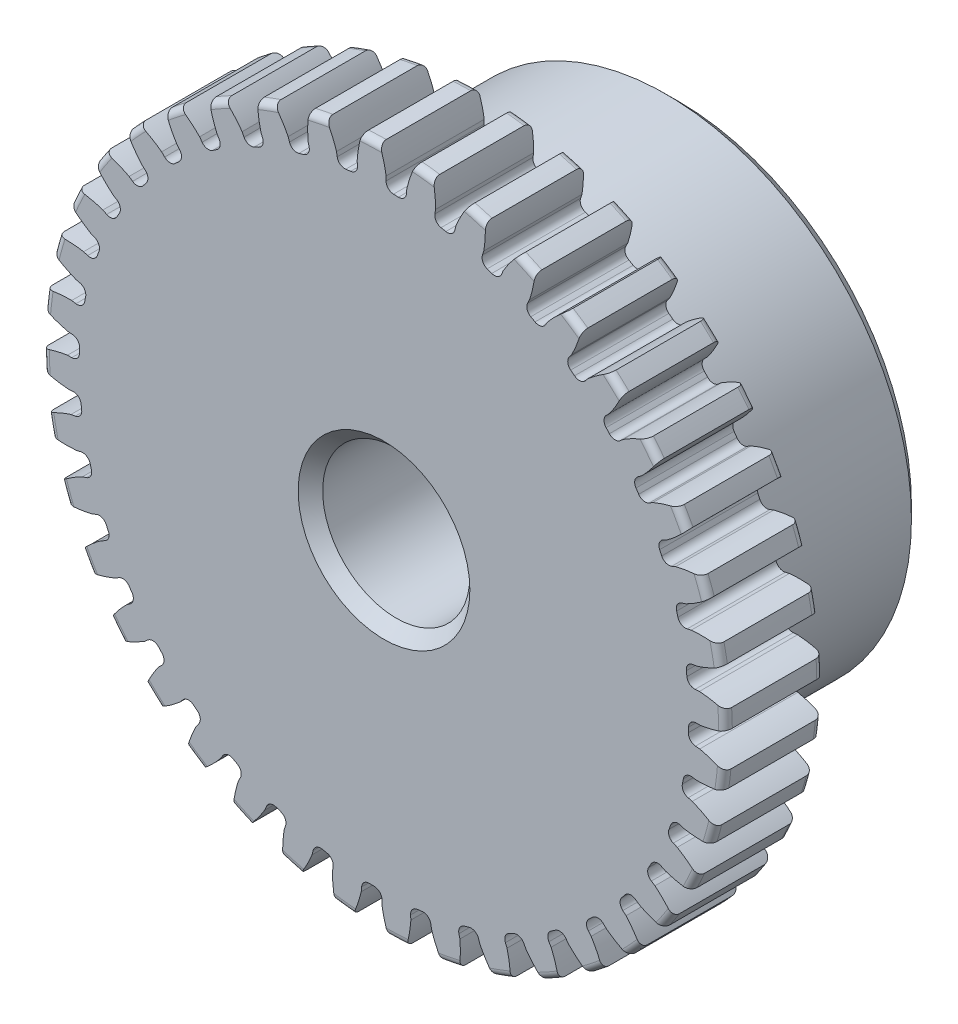
SolidWorks part; units mm, degrees
ref_plane "Front" through (0, 0, 0) normal (0, 0, 1) x (1, 0, 0)
ref_plane "Top" through (0, 0, 0) normal (0, 1, 0) x (1, 0, 0)
ref_plane "Right" through (0, 0, 0) normal (1, 0, 0) x (0, 0, -1)
sketch "Sketch1" plane through (0, 0, 0) normal (0, 0, 1) x (1, 0, 0)
  line L0 (-508, 0) -> (508, 0) construction
  circle A0 centre (0, 0) radius 11.049
  circle A1 centre (0, 0) radius 10.5791 construction
  circle A3 centre (0, 0) radius 9.8589 construction
  dimension "D1" = 1.1901
  dimension "OD" = 22.098
  dimension "Ptich Dia" = 21.1582
  dimension "Root Dia" = 19.7177
  dimension "D3" = 0.4699
  dimension "Number of Teeth" = 1016
extrude "Boss-Extrude1" add sketch "Sketch1" against normal blind 3.175
sketch "Sketch2" plane through (0, 0, 0) normal (1, 0, 0) x (0, 0, -1)
  line L0 (3.175, 0) -> (9.525, 0)
  line L1 (3.175, 0) -> (3.175, 7.9375)
  line L2 (3.175, 7.9375) -> (9.525, 7.9375)
  line L3 (9.525, 7.9375) -> (9.525, 0)
  point P5 (9.525, -7.9375)
  point P6 (0, -11.049)
  point P7 (3.175, -11.049)
  point P9 (0, 11.049)
  dimension "Face Wd" = 3.175
  dimension "B Hub Dia" = 15.875
  dimension "D O'all Lg." = 9.525
revolve "Revolve1" add sketch "Sketch2" angle 360 about L0
fillet "Fillet2" radius 0.221 3 edges at (11.049, 0, -3.175) (11.049, 0, 0) (7.9375, 0, -3.175)
sketch "Sketch3" plane through (0, 0, 0) normal (0, 0, 1) x (1, 0, 0)
  line L0 (0, 0) -> (0, 11.049) construction
  line L1 (-2.5644, 9.9159) -> (0, 10.5791)
  line L2 (-9.5921, 10.5791) -> (9.5921, 10.5791) construction
  line L3 (-9.2865, 8.1774) -> (9.2865, 12.9808) construction
  line L4 (-2.5644, 9.9159) -> (0, 0) construction
  line L5 (-6.541, 7.8814) -> (0, 0) construction
  line L6 (-6.541, 7.8814) -> (-1.0572, 12.4326) construction
  line L7 (-1.7882, 10.0848) -> (0, 0) construction
  line L8 (-1.7882, 10.0848) -> (0.0375, 10.4085) construction
  arc A0 (-2.5644, 9.9159) -> (-6.541, 7.8814) centre (0, 0) ccw
  circle A1 centre (0, 0) radius 10.5791 construction
  circle A2 centre (0, 0) radius 10.2421 construction
  arc A3 (-2.5644, 9.9159) -> (-1.7882, 10.0848) centre (0, 0) cw
  circle A4 centre (0, 0) radius 11.049 construction
  point P6 (0, 10.5791)
  dimension "D1" = 2.6488
  dimension "Pressure Angle" = 14.5
  dimension "D2" = 4.503
  dimension "D3" = 7.1263
  dimension "D4" = 0.7946
  dimension "D5" = 1.8542
sketch "Sketch4" plane through (0, 0, 0) normal (0, 0, 1) x (1, 0, 0)
  line L0 (0, 0) -> (0.415, 10.5628) construction
  line L1 (0.0664, 10.2419) -> (0.0664, 9.8586)
  line L2 (0, 10.5791) -> (0.83, 10.5465) construction
  line L3 (0.7373, 10.2156) -> (0.7073, 9.8334)
  line L4 (0.0664, 9.8586) -> (0, 0) construction
  line L5 (0, 0) -> (0, 11.049) construction
  line L6 (-6.541, 7.8814) -> (-1.0572, 12.4326) construction
  line L7 (-6.541, 7.8814) -> (-1.0572, 12.4326) construction
  arc A0 (0.7073, 9.8334) -> (0.0664, 9.8586) centre (0, 0) ccw
  arc A1 (0, 10.5791) -> (0.83, 10.5465) centre (0, 0) cw construction
  circle A2 centre (0, 0) radius 10.5791 construction
  circle A3 centre (0, 0) radius 10.2421 construction
  circle A4 centre (0, 0) radius 9.8589 construction
  arc A5 (2.0294, 12.3113) -> (-1.0572, 12.4326) centre (0, 0) ccw
  spline S0 degree 2 poles (-1.0572, 12.4326) (-0.119, 11.4678) (0.0664, 10.2419) knots 0 0 0 1 1 1
  spline S1 degree 2 poles (2.0294, 12.3113) (1.0184, 11.4231) (0.7373, 10.2156) knots 0 0 0 1 1 1
  dimension "D1" = 0.8309
extrude "Cut-Extrude1" cut sketch "Sketch4" against normal through all
fillet "Fillet1" radius 0.2493 2 edges at (0.7073, 9.8334, -1.5875) (0.0664, 9.8586, -1.5875)
pattern_circular "CirPattern1" count 40 over 360 about axis through (0, 0, -3.175) along (0, 0, 1) of "Cut-Extrude1", "Fillet1"
sketch "Sketch5" plane through (0, 0, 0) normal (0, 0, 1) x (1, 0, 0)
  circle A0 centre (0, 0) radius 2.3813
  circle A1 centre (0, 0) radius 1.5875 construction
  dimension "Bore Min" = 4.7625
  dimension "Bore Max" = 3.175
extrude "Cut-Extrude2" cut sketch "Sketch5" against normal through all
chamfer "Chamfer1" distance 0.3969 angle 45 3 edges at (7.9375, 0, -9.525) (2.3813, 0, 0) (2.3813, 0, -9.525)
sketch "Pitch Dia" plane through (0, 0, 0) normal (0, 0, 1) x (1, 0, 0)
  circle A0 centre (0, 0) radius 10.5791 construction
  circle A1 centre (0, 0) radius 10.5791 construction
equation "\"D1@Boss-Extrude1\" = \"Face Wd@Sketch2\""
equation "\"D2@Sketch3\" = \"D1@Sketch3\"*1.7"
equation "\"D3@Sketch3\" = \"D1@Sketch3\"+\"D2@Sketch3\"-.001"
equation "\"D4@Sketch3\" = \"D1@Sketch3\"*.3"
equation "\"D5@Sketch3\" = \"D1@Sketch3\"-\"D4@Sketch3\""
equation "\"D1@Sketch4\" = 1.5708/(\"Number of Teeth@Sketch1\"/\"Ptich Dia@Sketch1\")"
equation "\"D1@Chamfer1\" = \"B Hub Dia@Sketch2\"*.025"
equation "\"D1@CirPattern1\" = \"Number of Teeth@Sketch1\""
equation "\"D1@Fillet1\" = \"D1@Sketch4\"*.3"
equation "\"D1@Fillet2\" = \"OD@Sketch1\"*.01"
equation "\"D1@Sketch1\" = 2.250/(\"Number of Teeth@Sketch1\"/\"Ptich Dia@Sketch1\")"
